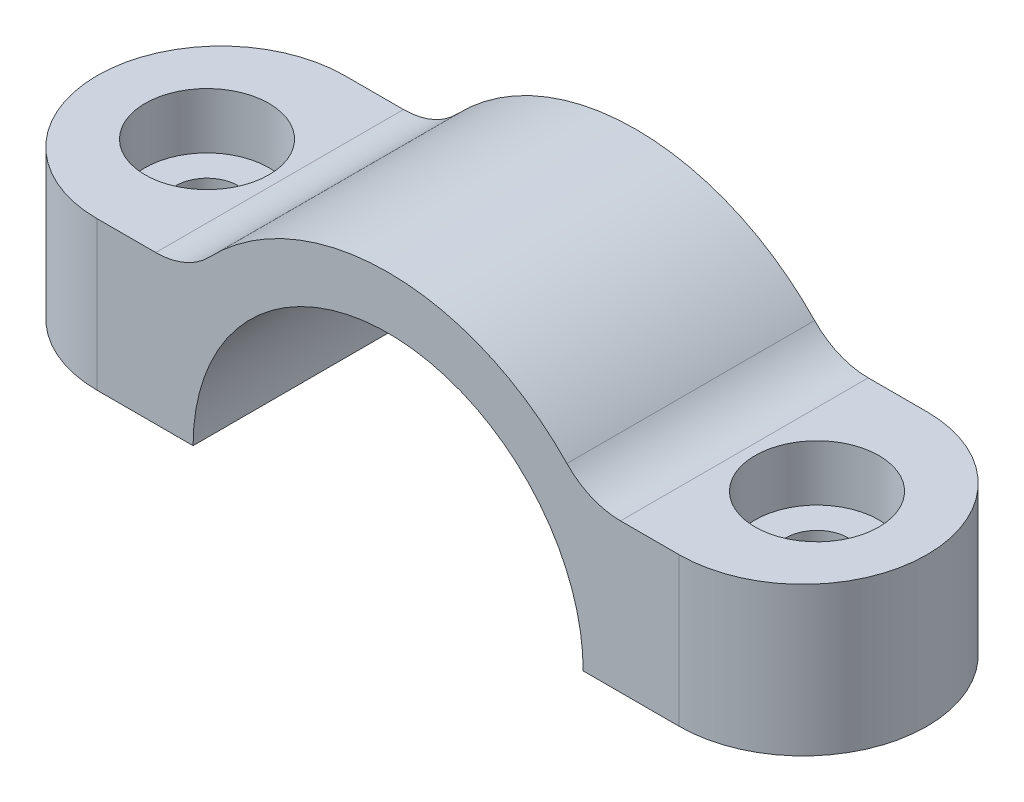
SolidWorks part; units mm, degrees
material "6061 Alloy"
ref_plane "Front Plane" through (0, 0, 0) normal (0, 0, 1) x (1, 0, 0)
ref_plane "Top Plane" through (0, 0, 0) normal (0, 1, 0) x (1, 0, 0)
ref_plane "Right Plane" through (0, 0, 0) normal (1, 0, 0) x (0, 0, -1)
sketch "Sketch1" plane through (0, 0, 0) normal (0, 0, 1) x (1, 0, 0)
  line L0 (-70.121, 0) -> (106.4801, 0) construction
  line L1 (0, -51.8235) -> (0, 43.3239) construction
  line L2 (-42.545, 0) -> (-42.545, 15.24)
  line L3 (-42.545, 15.24) -> (-20.32, 15.24)
  line L4 (-42.545, 0) -> (-20, 0)
  line L5 (42.545, 0) -> (20, 0)
  line L6 (42.545, 0) -> (42.545, 15.24)
  line L7 (42.545, 15.24) -> (20.32, 15.24)
  arc A0 (20, 0) -> (-20, 0) centre (0, 0) ccw
  arc A1 (20.32, 15.24) -> (-20.32, 15.24) centre (0, 0) ccw
  dimension "D1" = 40
  dimension "D2" = 50.8
  dimension "D3" = 15.24
  dimension "D4" = 42.545
extrude "Boss-Extrude1" add sketch "Sketch1" along normal mid plane 25.4
fillet "Fillet1" radius 7.62 1 edges at (20.32, 15.24, 0)
fillet "Fillet2" radius 7.62 1 edges at (-20.32, 15.24, 0)
sketch "Sketch2" plane through (0, 0, 0) normal (0, -1, 0) x (1, 0, 0)
  line L0 (-42.545, 12.7) -> (-20, -12.7) construction
  circle A0 centre (-31.2725, 0) radius 3.175
  dimension "D1" = 6.35
extrude "Cut-Extrude1" cut sketch "Sketch2" against normal blind 9.525
sketch "Sketch3" plane through (0, 9.525, 0) normal (0, -1, 0) x (1, 0, 0)
  circle A0 centre (-31.2725, 0) radius 6.35
  dimension "D1" = 12.7
extrude "Cut-Extrude2" cut sketch "Sketch3" against normal up to next (5.715 mm away)
mirror "Mirror1" about plane through (0, 0, 0) normal (1, 0, 0) of "Cut-Extrude1", "Cut-Extrude2"
sketch "Sketch4" plane through (0, 0, 0) normal (0, 1, 0) x (1, 0, 0)
  line L0 (-42.545, -12.7) -> (-42.545, 12.7) construction
  line L1 (-42.545, -12.7) -> (-42.545, 12.7) construction
  line L2 (42.545, -12.7) -> (42.545, 12.7) construction
  line L3 (42.545, -12.7) -> (42.545, 12.7) construction
  line L4 (-29.845, -12.7) -> (29.845, -12.7)
  line L5 (29.845, 12.7) -> (-29.845, 12.7)
  line L6 (0, 15.6188) -> (0, -20.4922) construction
  arc A0 (-29.845, 12.7) -> (-29.845, -12.7) centre (-29.845, 0) ccw
  arc A1 (29.845, 12.7) -> (29.845, -12.7) centre (29.845, 0) cw
extrude "Cut-Extrude3" cut sketch "Sketch4" along normal through all flip side to cut
